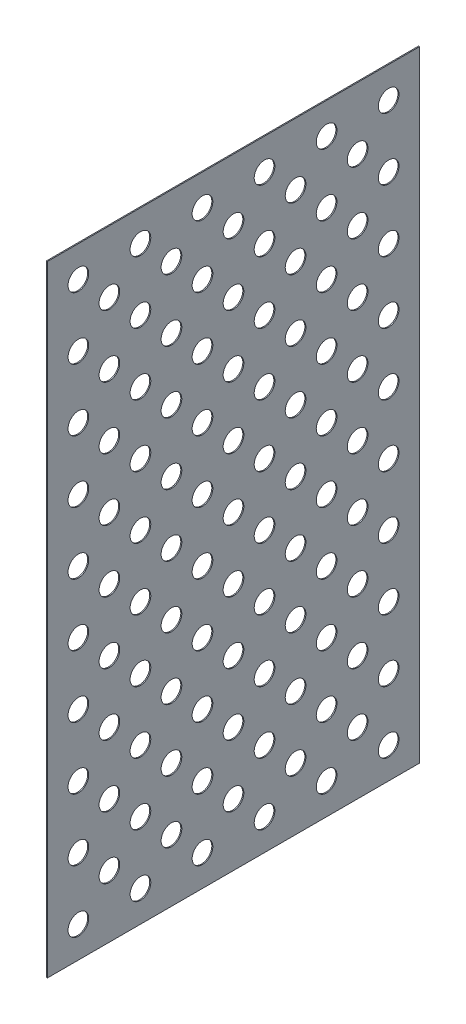
SolidWorks part; units mm, degrees
material "Balsa"
ref_plane "Front Plane" through (0, 0, 0) normal (0, 0, 1) x (1, 0, 0)
ref_plane "Top Plane" through (0, 0, 0) normal (0, 1, 0) x (1, 0, 0)
ref_plane "Right Plane" through (0, 0, 0) normal (1, 0, 0) x (0, 0, -1)
sketch "Sketch1" plane through (0, 0, 0) normal (1, 0, 0) x (0, 0, -1)
  line L1 (-457.2, -762) -> (457.2, -762)
  line L2 (-457.2, -762) -> (-457.2, 762)
  line L3 (-457.2, 762) -> (457.2, 762)
  line L4 (457.2, -762) -> (457.2, 762)
  line L5 (-457.2, -762) -> (457.2, 762) construction
  line L6 (-457.2, 762) -> (457.2, -762) construction
  point P0 (0, 0)
  dimension "D1" = 914.4
  dimension "D2" = 1524
extrude "Boss-Extrude1" add sketch "Sketch1" along normal blind 2.54
sketch "Sketch2" plane through (0, 0, 0) normal (-1, 0, 0) x (0, 0, 1)
  line L0 (-457.2, -717.55) -> (457.2, -717.55) construction
  line L1 (-457.2, -762) -> (-457.2, 762) construction
  line L2 (457.2, 762) -> (457.2, -762) construction
  line L3 (-457.2, -239.1833) -> (457.2, -239.1833) construction
  line L4 (-457.2, 239.1833) -> (457.2, 239.1833) construction
  line L5 (-457.2, 717.55) -> (457.2, 717.55) construction
  line L6 (457.2, -762) -> (-457.2, -762) construction
  line L7 (-457.2, 762) -> (457.2, 762) construction
  line L8 (-457.2, -717.55) -> (-457.2, -239.1833) construction
  line L9 (-457.2, -239.1833) -> (-457.2, 239.1833) construction
  line L10 (-457.2, 239.1833) -> (-457.2, 717.55) construction
  dimension "D1" = 44.45
  dimension "D2" = 44.45
ref_plane "Plane1" through (0, -239.1833, 0) normal (0, -1, 0) x (0, 0, 1)
ref_plane "Plane2" through (0, 239.1833, 0) normal (0, -1, 0) x (-1, 0, 0)
sketch "Sketch3" plane through (0, 0, 0) normal (-1, 0, 0) x (0, 0, 1)
  line L1 (457.2, -762) -> (-457.2, -762) construction
  line L2 (-457.2, -762) -> (-457.2, 762) construction
  circle A163 centre (-381, -685.8) radius 25.4
  circle A164 centre (-304.8, -609.6) radius 25.4
  circle A165 centre (-228.6, -685.8) radius 25.4
  circle A166 centre (-76.2, -685.8) radius 25.4
  circle A167 centre (76.2, -685.8) radius 25.4
  circle A168 centre (228.6, -685.8) radius 25.4
  circle A169 centre (381, -685.8) radius 25.4
  circle A170 centre (-228.6, -533.4) radius 25.4
  circle A171 centre (-76.2, -533.4) radius 25.4
  circle A172 centre (76.2, -533.4) radius 25.4
  circle A173 centre (228.6, -533.4) radius 25.4
  circle A174 centre (381, -533.4) radius 25.4
  circle A175 centre (-228.6, -381) radius 25.4
  circle A176 centre (-76.2, -381) radius 25.4
  circle A177 centre (76.2, -381) radius 25.4
  circle A178 centre (228.6, -381) radius 25.4
  circle A179 centre (381, -381) radius 25.4
  circle A180 centre (-228.6, -228.6) radius 25.4
  circle A181 centre (-76.2, -228.6) radius 25.4
  circle A182 centre (76.2, -228.6) radius 25.4
  circle A183 centre (228.6, -228.6) radius 25.4
  circle A184 centre (381, -228.6) radius 25.4
  circle A185 centre (-228.6, -76.2) radius 25.4
  circle A186 centre (-76.2, -76.2) radius 25.4
  circle A187 centre (76.2, -76.2) radius 25.4
  circle A188 centre (228.6, -76.2) radius 25.4
  circle A189 centre (381, -76.2) radius 25.4
  circle A190 centre (-228.6, 76.2) radius 25.4
  circle A191 centre (-76.2, 76.2) radius 25.4
  circle A192 centre (76.2, 76.2) radius 25.4
  circle A193 centre (228.6, 76.2) radius 25.4
  circle A194 centre (381, 76.2) radius 25.4
  circle A195 centre (-228.6, 228.6) radius 25.4
  circle A196 centre (-76.2, 228.6) radius 25.4
  circle A197 centre (76.2, 228.6) radius 25.4
  circle A198 centre (228.6, 228.6) radius 25.4
  circle A199 centre (381, 228.6) radius 25.4
  circle A200 centre (-228.6, 381) radius 25.4
  circle A201 centre (-76.2, 381) radius 25.4
  circle A202 centre (76.2, 381) radius 25.4
  circle A203 centre (228.6, 381) radius 25.4
  circle A204 centre (381, 381) radius 25.4
  circle A205 centre (-228.6, 533.4) radius 25.4
  circle A206 centre (-76.2, 533.4) radius 25.4
  circle A207 centre (76.2, 533.4) radius 25.4
  circle A208 centre (228.6, 533.4) radius 25.4
  circle A209 centre (381, 533.4) radius 25.4
  circle A210 centre (-228.6, 685.8) radius 25.4
  circle A211 centre (-76.2, 685.8) radius 25.4
  circle A212 centre (76.2, 685.8) radius 25.4
  circle A213 centre (228.6, 685.8) radius 25.4
  circle A214 centre (381, 685.8) radius 25.4
  circle A215 centre (-381, -533.4) radius 25.4
  circle A216 centre (-381, -381) radius 25.4
  circle A217 centre (-381, -228.6) radius 25.4
  circle A218 centre (-381, -76.2) radius 25.4
  circle A219 centre (-381, 76.2) radius 25.4
  circle A220 centre (-381, 228.6) radius 25.4
  circle A221 centre (-381, 381) radius 25.4
  circle A222 centre (-381, 533.4) radius 25.4
  circle A223 centre (-381, 685.8) radius 25.4
  circle A224 centre (-152.4, -609.6) radius 25.4
  circle A225 centre (0, -609.6) radius 25.4
  circle A226 centre (152.4, -609.6) radius 25.4
  circle A227 centre (304.8, -609.6) radius 25.4
  circle A228 centre (-152.4, -457.2) radius 25.4
  circle A229 centre (0, -457.2) radius 25.4
  circle A230 centre (152.4, -457.2) radius 25.4
  circle A231 centre (304.8, -457.2) radius 25.4
  circle A232 centre (-152.4, -304.8) radius 25.4
  circle A233 centre (0, -304.8) radius 25.4
  circle A234 centre (152.4, -304.8) radius 25.4
  circle A235 centre (304.8, -304.8) radius 25.4
  circle A236 centre (-152.4, -152.4) radius 25.4
  circle A237 centre (0, -152.4) radius 25.4
  circle A238 centre (152.4, -152.4) radius 25.4
  circle A239 centre (304.8, -152.4) radius 25.4
  circle A240 centre (-152.4, 0) radius 25.4
  circle A241 centre (0, 0) radius 25.4
  circle A242 centre (152.4, 0) radius 25.4
  circle A243 centre (304.8, 0) radius 25.4
  circle A244 centre (-152.4, 152.4) radius 25.4
  circle A245 centre (0, 152.4) radius 25.4
  circle A246 centre (152.4, 152.4) radius 25.4
  circle A247 centre (304.8, 152.4) radius 25.4
  circle A248 centre (-152.4, 304.8) radius 25.4
  circle A249 centre (0, 304.8) radius 25.4
  circle A250 centre (152.4, 304.8) radius 25.4
  circle A251 centre (304.8, 304.8) radius 25.4
  circle A252 centre (-152.4, 457.2) radius 25.4
  circle A253 centre (0, 457.2) radius 25.4
  circle A254 centre (152.4, 457.2) radius 25.4
  circle A255 centre (304.8, 457.2) radius 25.4
  circle A256 centre (-152.4, 609.6) radius 25.4
  circle A257 centre (0, 609.6) radius 25.4
  circle A258 centre (152.4, 609.6) radius 25.4
  circle A259 centre (304.8, 609.6) radius 25.4
  circle A260 centre (-304.8, -457.2) radius 25.4
  circle A261 centre (-304.8, -304.8) radius 25.4
  circle A262 centre (-304.8, -152.4) radius 25.4
  circle A263 centre (-304.8, 0) radius 25.4
  circle A264 centre (-304.8, 152.4) radius 25.4
  circle A265 centre (-304.8, 304.8) radius 25.4
  circle A266 centre (-304.8, 457.2) radius 25.4
  circle A267 centre (-304.8, 609.6) radius 25.4
  dimension "D1" = 50.8
  dimension "D2" = 50.8
  dimension "D3" = 76.2
  dimension "D4" = 76.2
  dimension "D5" = 76.2
  dimension "D6" = 76.2
extrude "Cut-Extrude1" cut sketch "Sketch3" against normal through all
equation "\"D1@Sketch1\"=3ft"
equation "\"D2@Sketch1\"=5ft"
equation "\"D1@Boss-Extrude1\"=.1in"
equation "\"D1@Sketch2\"=3.5in/2"
equation "\"D2@Sketch2\"=\"D1@Sketch2\""
equation "\"D2@Sketch3\"=\"D1@Sketch3\""
